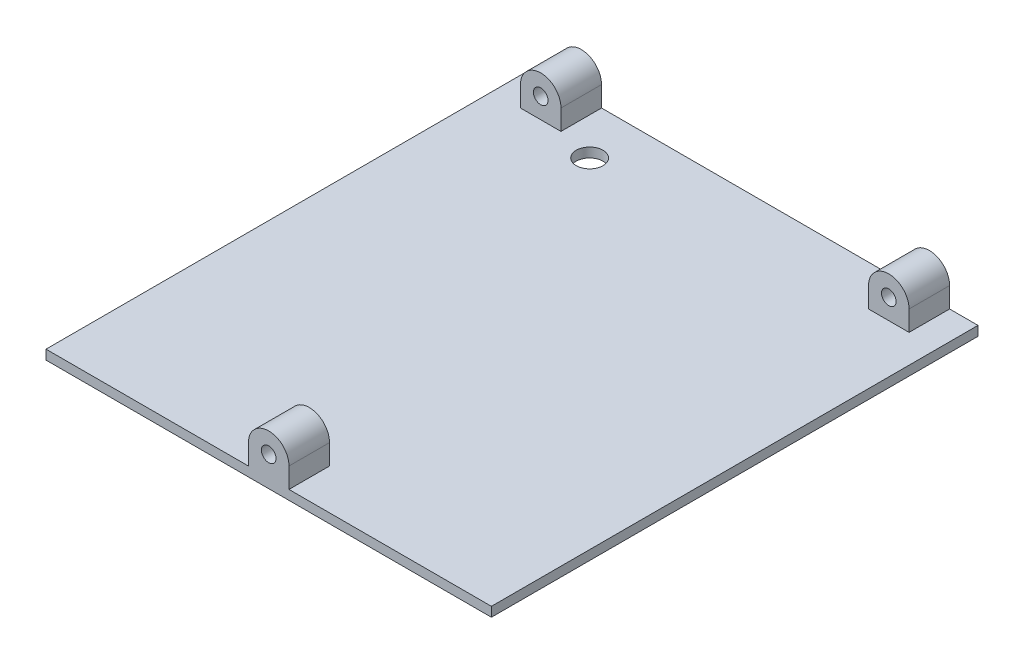
SolidWorks part; units mm, degrees
ref_plane "Front Plane" through (0, 0, 0) normal (0, 0, 1) x (1, 0, 0)
ref_plane "Top Plane" through (0, 0, 0) normal (0, 1, 0) x (1, 0, 0)
ref_plane "Right Plane" through (0, 0, 0) normal (1, 0, 0) x (0, 0, -1)
sketch "Sketch1" plane through (0, 0, 0) normal (0, 1, 0) x (1, 0, 0)
  line L1 (0, 0) -> (139.5, 0)
  line L2 (0, 0) -> (0, 152.4)
  line L3 (0, 152.4) -> (139.5, 152.4)
  line L4 (139.5, 0) -> (139.5, 152.4)
  dimension "D1" = 152.4
  dimension "D2" = 139.5
extrude "Boss-Extrude1" add sketch "Sketch1" along normal blind 6.35
sketch "Sketch2" plane through (0, 6.35, 0) normal (0, 1, 0) x (1, 0, 0)
  line L0 (0, 0) -> (139.5, 0) construction
  line L1 (0, 152.4) -> (139.5, 152.4)
  line L2 (0, 152.4) -> (0, 0)
  line L3 (0, 0) -> (139.5, 0)
  line L4 (139.5, 152.4) -> (139.5, 0)
  line L5 (139.5, 0) -> (139.5, 152.4) construction
extrude "Cut-Extrude1" cut sketch "Sketch2" against normal blind 3.375
sketch "Sketch3" plane through (0, 0, 0) normal (0, 0, 1) x (1, 0, 0)
  line L0 (63.4, 9.325) -> (63.4, 2.975)
  line L1 (63.4, 2.975) -> (76.1, 2.975)
  line L2 (76.1, 9.325) -> (76.1, 2.975)
  line L3 (0, 2.975) -> (139.5, 2.975) construction
  arc A0 (76.1, 9.325) -> (63.4, 9.325) centre (69.75, 9.325) ccw
  circle A1 centre (69.75, 9.325) radius 2.286
  point P6 (69.75, 2.975)
  point P9 (69.75, 2.975)
  dimension "D1" = 4.572
  dimension "D2" = 12.7
  dimension "D8" = 6.35
  dimension "D5" = 6.35
extrude "Boss-Extrude2" add sketch "Sketch3" against normal blind 12.7
sketch "Sketch4" plane through (0, 0, -152.4) normal (0, 0, -1) x (-1, 0, 0)
  line L0 (-130.61, 9.325) -> (-130.61, 2.975)
  line L1 (-130.61, 2.975) -> (-117.91, 2.975)
  line L2 (-117.91, 9.325) -> (-117.91, 2.975)
  line L3 (-21.59, 9.325) -> (-21.59, 2.975)
  line L4 (-21.59, 2.975) -> (-8.89, 2.975)
  line L5 (-8.89, 9.325) -> (-8.89, 2.975)
  line L6 (-139.5, 2.975) -> (0, 2.975) construction
  line L7 (0, 2.975) -> (0, 0) construction
  line L8 (-139.5, 2.975) -> (-139.5, 0) construction
  arc A0 (-117.91, 9.325) -> (-130.61, 9.325) centre (-124.26, 9.325) ccw
  circle A1 centre (-124.26, 9.325) radius 2.286
  arc A2 (-8.89, 9.325) -> (-21.59, 9.325) centre (-15.24, 9.325) ccw
  circle A3 centre (-15.24, 9.325) radius 2.286
  dimension "D1" = 4.572
  dimension "D3" = 6.35
  dimension "D5" = 4.572
  dimension "D7" = 6.35
  dimension "D2" = 6.35
  dimension "D4" = 12.7
  dimension "D6" = 6.35
  dimension "D8" = 12.7
  dimension "D9" = 8.89
  dimension "D10" = 8.89
  dimension "D11" = 15.24
  dimension "D12" = 15.24
extrude "Boss-Extrude3" add sketch "Sketch4" against normal blind 12.7
sketch "Sketch5" plane through (0, 0, 0) normal (0, -1, 0) x (1, 0, 0)
  line L0 (0, -152.4) -> (0, 0) construction
  line L1 (139.5, -152.4) -> (0, -152.4) construction
  circle A0 centre (33.274, -136.9916) radius 4.191
  dimension "D1" = 8.382
  dimension "D2" = 33.274
  dimension "D3" = 15.4084
extrude "Cut-Extrude2" cut sketch "Sketch5" against normal through all
